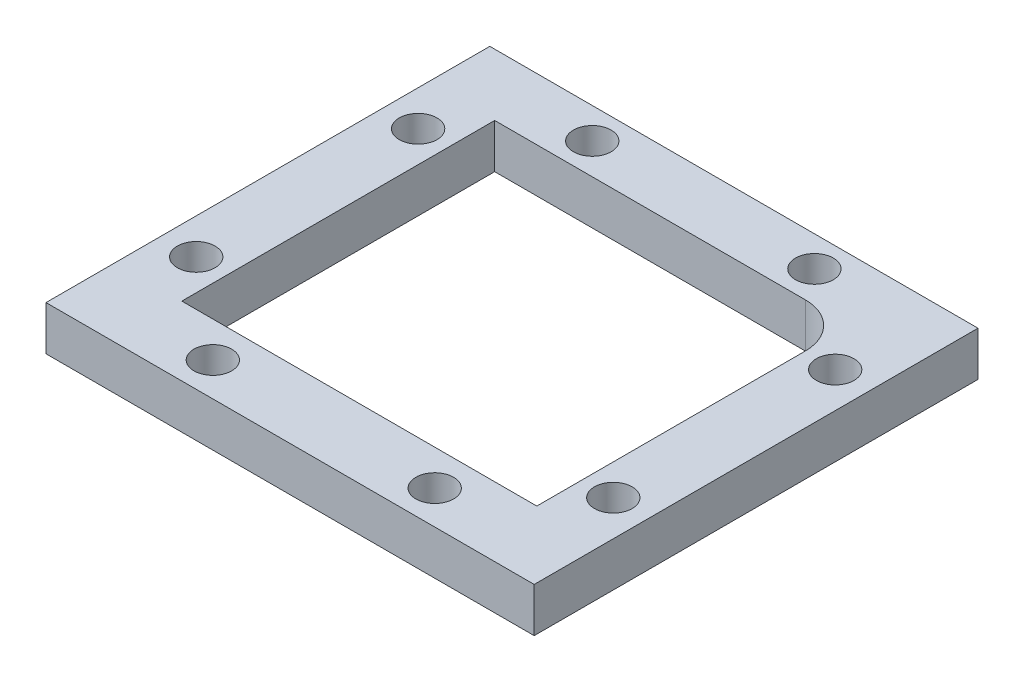
SolidWorks part; units mm, degrees
ref_plane "Alzado" through (0, 0, 0) normal (0, 0, 1) x (1, 0, 0)
ref_plane "Planta" through (0, 0, 0) normal (0, 1, 0) x (1, 0, 0)
ref_plane "Vista lateral" through (0, 0, 0) normal (1, 0, 0) x (0, 0, -1)
sketch "Croquis1" plane through (0, 0, 0) normal (0, 1, 0) x (1, 0, 0)
  line L0 (0, 20) -> (0, -20) construction
  line L1 (-20, 20) -> (20, 20)
  line L2 (-20, 20) -> (-20, -20)
  line L3 (-20, -20) -> (20, -20)
  line L4 (20, 20) -> (20, -20)
  line L5 (-20, 20) -> (20, -20) construction
  line L6 (-20, -20) -> (20, 20) construction
  line L7 (-20, -4.25) -> (-30, -7.25)
  line L8 (-30, -7.25) -> (-30, -15.25)
  line L9 (-30, -15.25) -> (30, -15.25)
  line L10 (20, -4.25) -> (30, -7.25)
  line L11 (30, -7.25) -> (30, -15.25)
  circle A0 centre (-15, 15) radius 2.125
  circle A1 centre (15, 15) radius 2.125
  circle A4 centre (0, 0) radius 15.25
  circle A5 centre (-15, -15) radius 2.125 [skipped]
  circle A6 centre (15, -15) radius 2.125 [skipped]
  point P0 (0, 0)
  point P25 (0, -15.25)
  dimension "D3" = 4.25
  dimension "D7" = 30.5
  dimension "D1" = 40
  dimension "D2" = 40
  dimension "D4" = 5
  dimension "D5" = 2
  dimension "D8" = 8
  dimension "D9" = 10
  dimension "D10" = 15.25
  dimension "D12" = 3
  dimension "D6" = 2
extrude "Soporte caja reductora" add sketch "Croquis1" against normal blind 20
sketch "Croquis3" plane through (0, 0, 15.25) normal (0, 0, 1) x (1, 0, 0)
  line L3 (-20, -20) -> (-20, 0) construction
  circle A0 centre (-23.5, -10) radius 2.125
  circle A1 centre (23.5, -10) radius 2.125
  dimension "D1" = 4.25
  dimension "D2" = 3.5
extrude "Cortar-Extruir1" cut sketch "Croquis3" against normal through all
fillet "Redondeo1" radius 5 2 edges at (-20, -10, -20) (20, -10, -20)
sketch "Sketch1" plane through (0, 0, 0) normal (0, 1, 0) x (1, 0, 0)
  line L0 (15, 20) -> (30, 20)
  line L1 (30, 20) -> (30, 8)
  line L2 (30, 8) -> (25.5, 8)
  line L4 (25.5, 8) -> (25.5, 15)
  line L5 (25.5, 15) -> (20, 15)
  circle A0 centre (15, 15) radius 5
  arc M37 (20, 15) -> (15, 20) centre (15, 15) ccw
  dimension "D1" = 12
  dimension "D2" = 5.5
extrude "Boss-Extrude1" add sketch "Sketch1" along direction (0, 1, 0) on the side against the normal up to surface (20 mm away) contours L5 L4 L2 L1 L0 M37
sketch "Sketch2" plane through (0, 0, -20) normal (0, 0, -1) x (-1, 0, 0)
  line L1 (-20, -20) -> (-20, 0) construction
  circle A0 centre (-22.75, -10) radius 1.625
  dimension "D1" = 3.25
  dimension "D2" = 2.75
extrude "Cut-Extrude1" cut sketch "Sketch2" against normal up to next
sketch "Sketch3" plane through (0, 0, -15) normal (0, 0, 1) x (1, 0, 0)
  line L1 (20, -11.5877) -> (22.75, -13.1754)
  line L2 (22.75, -13.1754) -> (25.5, -11.5877)
  line L3 (25.5, -11.5877) -> (25.5, -8.4123)
  line L4 (25.5, -8.4123) -> (22.75, -6.8246)
  line L5 (22.75, -6.8246) -> (20, -8.4123)
  line L6 (20, -8.4123) -> (20, -11.5877)
  circle A0 centre (22.75, -10) radius 2.75 construction
  dimension "D1" = 5.5
extrude "Cut-Extrude2" cut sketch "Sketch3" against normal blind 2
sketch "Sketch4" plane through (25.5, 0, 0) normal (-1, 0, 0) x (0, 0, 1)
  line L5 (-15, -8.4123) -> (-15, 0) construction
  line L6 (-20, 0) -> (-8, 0) construction
  circle A0 centre (-12.25, -10) radius 1.625
  dimension "D1" = 2.75
  dimension "D2" = 3.25
  dimension "D3" = 10
extrude "Cut-Extrude3" cut sketch "Sketch4" against normal through all
sketch "Sketch5" plane through (30, 0, 0) normal (1, 0, 0) x (0, 0, -1)
  line L1 (15, -11.5877) -> (15, -8.4123)
  line L2 (15, -8.4123) -> (12.25, -6.8246)
  line L3 (12.25, -6.8246) -> (9.5, -8.4123)
  line L4 (9.5, -8.4123) -> (9.5, -11.5877)
  line L5 (9.5, -11.5877) -> (12.25, -13.1754)
  line L6 (12.25, -13.1754) -> (15, -11.5877)
  circle A0 centre (12.25, -10) radius 2.75 construction
  dimension "D1" = 5.5
extrude "Cut-Extrude4" cut sketch "Sketch5" along normal blind 2 from surface
sketch "Croquis6" plane through (0, 0, 0) normal (0, 1, 0) x (1, 0, 0)
  line L0 (-20, -20) -> (20, -20) construction
  line L1 (-15.25, 0) -> (15.25, 0)
  line L2 (-15.25, 0) -> (-15.25, -20)
  line L3 (-15.25, -20) -> (15.25, -20)
  line L4 (15.25, 0) -> (15.25, -20)
  line L6 (-20, -20) -> (20, -20)
  line L7 (-20, -20) -> (-20, -15.25)
  line L8 (-20, -15.25) -> (20, -15.25)
  line L9 (20, -20) -> (20, -15.25)
  circle A0 centre (0, 0) radius 15.25 construction
  circle M5 centre (0, 0) radius 15.25
  line M14 (-20, -15.25) -> (-20, -20)
  line M15 (-20, -20) -> (20, -20)
  line M16 (20, -20) -> (20, -15.25)
extrude "Cortar-Extruir17" cut sketch "Croquis6" against normal through all contours L8 L2 L4 M15 | L8 L2 M14 M15 | L2 L8 M5 | L8 L4 M5 | L8 L4 M15 M16
mirror "Simetría1" about plane through (0, 0, 0) normal (0, 1, 0) of bodies 111
sketch "Croquis7" plane through (0, 0, -20) normal (0, 0, -1) x (-1, 0, 0)
  line L1 (-30, 0) -> (30, 0)
  line L2 (-30, 0) -> (-30, -20)
  line L3 (-30, -20) -> (30, -20)
  line L4 (30, 0) -> (30, -20)
extrude "Cortar-Extruir18" cut sketch "Croquis7" against normal through all
sketch "Croquis8" plane through (0, 20, 0) normal (0, 1, 0) x (1, 0, 0)
  line L3 (-15, 20) -> (30, 20) construction
  line L4 (-11.0405, 13.9391) -> (-10.3152, 11.2321)
  line L5 (10.8174, 13.8793) -> (10.3152, 11.2321)
  line L59 (10.8174, 13.8793) -> (11.9787, 20)
  line L60 (-11.0405, 13.9391) -> (-12.6645, 20)
  line L61 (11.9787, 20) -> (-12.6645, 20)
  circle A0 centre (0, 0) radius 15.25
extrude "Saliente-Extruir2" add sketch "Croquis8" along normal blind 49
sketch "Croquis9" plane through (0, 69, 0) normal (0, 1, 0) x (1, 0, 0)
  line L0 (-20, 0) -> (20, 0)
  line L1 (-20, 15) -> (-20, -4.25) construction
  line L2 (20, 15) -> (20, -4.25) construction
  line L3 (-20, 0) -> (-20, 15)
  line L4 (-15, 20) -> (12.6645, 20)
  line L5 (12.6645, 20) -> (20, 13.9368)
  line L6 (20, 13.9368) -> (20, 0)
  line L7 (20, 0) -> (20.1759, -0.147)
  line L8 (-14.75, 0) -> (-14.75, -15.25)
  line L9 (-15.25, -15.25) -> (-30, -15.25)
  line L10 (-30, -15.25) -> (-30, -7.25)
  line L11 (-30, -7.25) -> (-20, -4.25)
  line L12 (-20, -4.25) -> (-20, 0)
  line L13 (-14.75, -15.25) -> (-15.25, -15.25)
  line L14 (-14.75, -15.25) -> (0, -15.25)
  line L15 (0, -15.25) -> (0, -14.75)
  circle A0 centre (0, 0) radius 14.75
  circle A1 centre (-15, 15) radius 5
  dimension "D1" = 29.5
extrude "Soporte motor" add sketch "Croquis9" against normal blind 15 from offset 15 offset against normal yes
sketch "Croquis12" plane through (0, 0, 15.25) normal (0, 0, 1) x (1, 0, 0)
  line L1 (0, 54) -> (-30, 54) construction
  line L2 (-20, 39) -> (-20, 54) construction
  circle A0 centre (-23.5, 46.5) radius 2.125
  dimension "D3" = 4.25
  dimension "D1" = 7.5
  dimension "D2" = 3.5
extrude "Agujeros de sujecion a base" cut sketch "Croquis12" against normal through all
sketch "Croquis13" plane through (0, 0, 15.25) normal (0, 0, 1) x (1, 0, 0)
  line L1 (-20, 44.4793) -> (-20, 48.5207)
  line L2 (-20, 48.5207) -> (-23.5, 50.5415)
  line L3 (-23.5, 50.5415) -> (-27, 48.5207)
  line L4 (-27, 48.5207) -> (-27, 44.4793)
  line L5 (-27, 44.4793) -> (-23.5, 42.4585)
  line L6 (-23.5, 42.4585) -> (-20, 44.4793)
  circle A0 centre (-23.5, 46.5) radius 3.5 construction
  dimension "D1" = 7
extrude "Tuerca Agujero de sujecion a base" cut sketch "Croquis13" against normal blind 10 from offset 4 offset against normal yes
sketch "Croquis10" plane through (0, 69, 0) normal (0, 1, 0) x (1, 0, 0)
  line L0 (-10.3152, 11.2321) -> (-9.8079, 9.3388)
  line L1 (10.3152, 11.2321) -> (9.4813, 8.1201)
  circle A0 centre (0, 0) radius 14.75
  circle A1 centre (0, 0) radius 15.25
  arc M2 (-10.3152, 11.2321) -> (10.3152, 11.2321) centre (0, 0) cw
extrude "Saliente-Extruir4" add sketch "Croquis10" against normal up to surface (15 mm away) contours A0 L1 L0 M2
sketch "Croquis11" plane through (0, 0, 0) normal (0, -1, 0) x (1, 0, 0)
  line L0 (0, 0) -> (0, -12.6937) construction
  line L1 (15, -20) -> (30, -20)
  line L2 (30, -20) -> (30, 15.25)
  line L3 (30, 15.25) -> (15.25, 15.25)
  line L4 (15.25, 0) -> (15.25, 15.25) construction
  line L5 (15.25, 15.25) -> (30, 15.25) construction
  line L6 (15.25, 15.25) -> (15.25, 4.25)
  line L7 (15.25, 4.25) -> (20, 4.25)
  line L8 (20, 4.25) -> (20, -15)
  circle A0 centre (0, 0) radius 22.5
  circle A1 centre (-15, -15) radius 5
  circle A2 centre (15, -15) radius 5
  line M8 (-15, -20) -> (30, -20)
  line M9 (30, -20) -> (30, -8)
  line M10 (30, -8) -> (25.5, -8)
  line M11 (25.5, -8) -> (25.5, -15)
  line M12 (25.5, -15) -> (20, -15)
  line M14 (20, 4.25) -> (30, 7.25)
  line M15 (30, 7.25) -> (30, 15.25)
  line M16 (30, 15.25) -> (15.25, 15.25)
  line M17 (15.25, 15.25) -> (15.25, 0)
  dimension "D1" = 45
extrude "Cortar-Extruir19" cut sketch "Croquis11" against normal blind 25 contours A0 L3 L7 M14 M17 | A0 M14 M15 M16 | A2 M12 M8 M9 M10 M11
mirror "Simetría2"
sketch "Croquis14" plane through (0, 0, 15.25) normal (0, 0, 1) x (1, 0, 0)
  line L1 (-30, 20) -> (20, 20)
  line L2 (-30, 20) -> (-30, 138)
  line L3 (-30, 138) -> (20, 138)
  line L4 (20, 20) -> (20, 138)
extrude "Cortar-Extruir22" cut sketch "Croquis14" against normal through all
sketch "Croquis15" plane through (0, 0, 0) normal (0, -1, 0) x (1, 0, 0)
  line L0 (-30, 7.25) -> (-30, 15.25) construction
  line L1 (-20, 4.25) -> (-30, 4.25)
  line L2 (-20, 4.25) -> (-20, 11.25)
  line L3 (-20, 11.25) -> (-30, 11.25)
  line L4 (-30, 4.25) -> (-30, 11.25)
  line L5 (-30, 15.25) -> (-15.25, 15.25) construction
  dimension "D1" = 4
extrude "Cortar-Extruir23" cut sketch "Croquis15" against normal through all
sketch "Croquis16" plane through (0, 0, 0) normal (0, -1, 0) x (1, 0, 0)
  line L0 (-15.25, 0) -> (-15.25, 15.25) construction
  line L1 (-30, 15.25) -> (-15.25, 15.25)
  line L2 (-30, 15.25) -> (-30, 12.75)
  line L3 (-20, 12.75) -> (-15.25, 12.75)
  line L4 (-15.25, 15.25) -> (-15.25, 12.75)
  line L5 (-30, 12.75) -> (-30, 11.25)
  line L6 (-30, 11.25) -> (-20, 11.25)
  line L7 (-20, 11.25) -> (-30, 11.25) construction
  line L8 (-20, -15) -> (-20, 11.25) construction
  line L9 (-20, 11.25) -> (-20, 12.75)
  dimension "D1" = 2.5
extrude "Cortar-Extruir24" cut sketch "Croquis16" against normal through all
sketch "Croquis18" plane through (0, 0, -20) normal (0, 0, -1) x (-1, 0, 0)
  line L0 (20, 0) -> (20, 20) construction
  line L1 (-20, 0) -> (20, 0)
  line L2 (-20, 0) -> (-20, 10)
  line L3 (-20, 10) -> (20, 10)
  line L4 (20, 0) -> (20, 10)
  line L5 (15, 20) -> (-15, 20) construction
  dimension "D1" = 10
extrude "Cortar-Extruir25" cut sketch "Croquis18" against normal through all
sketch "Croquis19" plane through (0, 20, 0) normal (0, 1, 0) x (1, 0, 0)
  line L0 (-20, -12.75) -> (-34, -12.75)
  line L1 (-34, -12.75) -> (-34, -7.75)
  line L2 (-34, -7.75) -> (-24, -7.75)
  line L3 (-24, -7.75) -> (-20, -3.75)
  line L4 (-20, 15) -> (-20, -12.75) construction
  line L5 (-20, -3.75) -> (-20, -12.75)
  dimension "D1" = 5
  dimension "D2" = 4
  dimension "D3" = 4
  dimension "D4" = 10
extrude "Saliente-Extruir5" add sketch "Croquis19" against normal up to surface (10 mm away) up to face at (15, 10, -12.875)
sketch "Croquis20" plane through (0, 0, 7.75) normal (0, 0, -1) x (-1, 0, 0)
  circle A0 centre (29, 15) radius 1
  dimension "D1" = 2
extrude "Cortar-Extruir26" cut sketch "Croquis20" against normal through all
sketch "Croquis21" plane through (20, 0, 0) normal (1, 0, 0) x (0, 0, -1)
  line L1 (20, 20) -> (20, 10) construction
  circle A0 centre (4.75, 15) radius 1.625
  dimension "D1" = 3.25
  dimension "D2" = 15.25
extrude "Cortar-Extruir27" cut sketch "Croquis21" against normal up to next
sketch "Croquis22" plane through (0, 10, 0) normal (0, -1, 0) x (1, 0, 0)
  circle A0 centre (-15, -15) radius 2.125
  circle A1 centre (15, -15) radius 2.125
  circle A2 centre (15, -15) radius 1
  circle A3 centre (-15, -15) radius 1
  dimension "D1" = 2
extrude "Saliente-Extruir6" add sketch "Croquis22" against normal blind 10
sketch "Croquis23" plane through (0, 0, -20) normal (0, 0, -1) x (-1, 0, 0)
  circle A0 centre (0, 15) radius 1.625
  dimension "D1" = 3.25
extrude "Cortar-Extruir28" cut sketch "Croquis23" against normal through all
sketch "Croquis24" plane through (0, 0, -20) normal (0, 0, -1) x (-1, 0, 0)
  line L1 (1.5877, 12.25) -> (3.1754, 15)
  line L2 (3.1754, 15) -> (1.5877, 17.75)
  line L3 (1.5877, 17.75) -> (-1.5877, 17.75)
  line L4 (-1.5877, 17.75) -> (-3.1754, 15)
  line L5 (-3.1754, 15) -> (-1.5877, 12.25)
  line L6 (-1.5877, 12.25) -> (1.5877, 12.25)
  circle A0 centre (0, 15) radius 2.75 construction
  dimension "D1" = 5.5
extrude "Cortar-Extruir29" cut sketch "Croquis24" against normal blind 10 from offset 3 offset against normal yes
sketch "Croquis26" plane through (0, 10, 0) normal (0, -1, 0) x (1, 0, 0)
  line L0 (-29, 12.75) -> (-58.825, 12.75)
  line L1 (-58.825, 12.75) -> (-39.1605, -4.1045)
  line L3 (-39.5945, 1.5357) -> (-46.8449, 7.75)
  line L4 (-46.8449, 7.75) -> (-34.2682, 7.75)
  line L5 (-34.2682, 7.75) -> (-39.5945, 1.5357)
  line L7 (-29, 7.75) -> (-35.7321, -0.1045)
  line L8 (-29, 7.75) -> (-29, 12.75)
  line L9 (-34, 7.75) -> (-24, 7.75) construction
  line L10 (-34, 12.75) -> (-15.25, 12.75) construction
  line L11 (-39.1605, -4.1045) -> (-20, -4.1045)
  line L12 (-20, 3.75) -> (-20, -15) construction
  line L13 (-20, -4.1045) -> (-20, -0.1045)
  line L14 (-20, -0.1045) -> (-35.7321, -0.1045)
  dimension "D1" = 4
  dimension "D2" = 4
  dimension "D3" = 4
  dimension "D4" = 29.825
  dimension "D5" = 40.6
extrude "Saliente-Extruir7" add sketch "Croquis26" against normal blind 10
sketch "Croquis27" plane through (0, 0, 12.75) normal (0, 0, 1) x (1, 0, 0)
  line L0 (-29, 16) -> (-29, 14) construction
  line L1 (-46.8449, 20) -> (-46.8449, 10) construction
  circle A0 centre (-40.5449, 15) radius 1.625
  circle A2 centre (-29, 15) radius 1.625
  dimension "D1" = 3.25
  dimension "D2" = 6.3
extrude "Cortar-Extruir30" cut sketch "Croquis27" against normal up to next
sketch "Croquis28" plane through (0, 0, 12.75) normal (0, 0, 1) x (1, 0, 0)
  line L1 (-38.9572, 12.25) -> (-37.3694, 15)
  line L2 (-37.3694, 15) -> (-38.9572, 17.75)
  line L3 (-38.9572, 17.75) -> (-42.1326, 17.75)
  line L4 (-42.1326, 17.75) -> (-43.7203, 15)
  line L5 (-43.7203, 15) -> (-42.1326, 12.25)
  line L6 (-42.1326, 12.25) -> (-38.9572, 12.25)
  line L7 (-27.4123, 12.25) -> (-25.8246, 15)
  line L8 (-25.8246, 15) -> (-27.4123, 17.75)
  line L9 (-27.4123, 17.75) -> (-30.5877, 17.75)
  line L10 (-30.5877, 17.75) -> (-32.1754, 15)
  line L11 (-32.1754, 15) -> (-30.5877, 12.25)
  line L12 (-30.5877, 12.25) -> (-27.4123, 12.25)
  circle A0 centre (-40.5449, 15) radius 2.75 construction
  circle A1 centre (-29, 15) radius 2.75 construction
  dimension "D1" = 5.5
extrude "Cortar-Extruir31" cut sketch "Croquis28" against normal up to next from offset 3 offset against normal yes
sketch "Croquis29" plane through (-18.6128, 0, -21.716) normal (-0.6508, 0, -0.7593) x (-0.7593, 0, 0.6508)
  line L2 (31.0624, 20) -> (31.0624, 10) construction
  circle A0 centre (33.8124, 15) radius 1.625
  dimension "D2" = 3.25
  dimension "D1" = 2.75
extrude "Cortar-Extruir32" cut sketch "Croquis29" against normal up to next
sketch "Croquis31" plane through (-18.6128, 0, -21.716) normal (-0.6508, 0, -0.7593) x (-0.7593, 0, 0.6508)
  line L1 (36.5624, 16.5877) -> (33.8124, 18.1754)
  line L2 (33.8124, 18.1754) -> (31.0624, 16.5877)
  line L3 (31.0624, 16.5877) -> (31.0624, 13.4123)
  line L4 (31.0624, 13.4123) -> (33.8124, 11.8246)
  line L5 (33.8124, 11.8246) -> (36.5624, 13.4123)
  line L6 (36.5624, 13.4123) -> (36.5624, 16.5877)
  circle A0 centre (33.8124, 15) radius 2.75 construction
  dimension "D1" = 5.5
extrude "Cortar-Extruir33" cut sketch "Croquis31" against normal up to next from offset 2.5 offset against normal yes
sketch "Croquis35" plane through (0, 20, 0) normal (0, 1, 0) x (1, 0, 0)
  line L0 (-15, 20) -> (15, 20) construction
  line L1 (10.3896, 0) -> (23.695, 0)
  line L2 (10.3896, 0) -> (10.3896, -6.8269)
  line L3 (10.3896, -6.8269) -> (23.695, -6.8269)
  line L4 (23.695, 0) -> (23.695, -6.8269)
  dimension "D1" = 20
extrude "Cortar-Extruir34" cut sketch "Croquis35" against normal through all both and the other way through all
sketch "Croquis36" plane through (20, 0, 0) normal (1, 0, 0) x (0, 0, -1)
  line L1 (7.5, 16.5877) -> (4.75, 18.1754)
  line L2 (4.75, 18.1754) -> (2, 16.5877)
  line L3 (2, 16.5877) -> (2, 13.4123)
  line L4 (2, 13.4123) -> (4.75, 11.8246)
  line L5 (4.75, 11.8246) -> (7.5, 13.4123)
  line L6 (7.5, 13.4123) -> (7.5, 16.5877)
  circle A0 centre (4.75, 15) radius 2.75 construction
  dimension "D1" = 5.5
extrude "Cortar-Extruir35" cut sketch "Croquis36" against normal blind 10 from offset 3 offset against normal yes
sketch "Croquis37" plane through (0, 10, 0) normal (0, -1, 0) x (1, 0, 0)
  line L0 (-39.1605, -4.1045) -> (-20.6149, -20)
  line L1 (-20.6149, -20) -> (-15, -20)
  line L2 (-33.014, -4.1045) -> (-19.5581, -15.6376)
  line L3 (-39.1605, -4.1045) -> (-20, -4.1045) construction
  line L4 (-19.5581, -15.6376) -> (-15, -20)
  line L5 (-58.825, 12.75) -> (-39.1605, -4.1045) construction
  line L6 (-39.5945, 1.5357) -> (-46.8449, 7.75) construction
  line L7 (-39.1605, -4.1045) -> (-33.014, -4.1045)
extrude "Saliente-Extruir8" add sketch "Croquis37" against normal blind 10
sketch "Croquis38" plane through (0, 10, 0) normal (0, -1, 0) x (1, 0, 0)
  line L0 (-58.825, 12.75) -> (-38.825, 12.75)
  line L1 (-58.825, 12.75) -> (-15.25, 12.75) construction
  line L2 (-38.825, 12.75) -> (-38.825, 9.75)
  line L3 (-38.825, 9.75) -> (-55.3248, 9.75)
  line L4 (-58.825, 12.75) -> (-20.6149, -20) construction
  line L5 (-55.3248, 9.75) -> (-58.825, 12.75)
  dimension "D1" = 3
  dimension "D2" = 20
extrude "Saliente-Extruir9" add sketch "Croquis38" along normal blind 13
sketch "Croquis39" plane through (0, 10, 0) normal (0, -1, 0) x (1, 0, 0)
  line L0 (-38.825, 9.75) -> (-38.825, 7.75)
  line L1 (-46.8449, 7.75) -> (-34.2682, 7.75) construction
  line L3 (-55.3248, 9.75) -> (-20.6149, -20) construction
  line L4 (-52.9914, 7.75) -> (-55.3248, 9.75)
  line L5 (-55.3248, 9.75) -> (-38.825, 9.75)
  line L6 (-52.9914, 7.75) -> (-50.658, 5.75)
  line L7 (-50.658, 5.75) -> (-38.825, 5.75)
  line L8 (-38.825, 5.75) -> (-38.825, 7.75)
  dimension "D1" = 2
extrude "Saliente-Extruir10" add sketch "Croquis39" along normal blind 3
mirror "Simetría3" of bodies 142
sketch "Croquis40" plane through (0, 0, -20) normal (0, 0, -1) x (-1, 0, 0)
  line L1 (-30.8963, 20) -> (75.6873, 20)
  line L2 (-30.8963, 20) -> (-30.8963, -27.3915)
  line L3 (-30.8963, -27.3915) -> (75.6873, -27.3915)
  line L4 (75.6873, 20) -> (75.6873, -27.3915)
extrude "Cortar-Extruir36" cut sketch "Croquis40" against normal through all both and the other way through all
sketch "Croquis41" plane through (0, 20, 0) normal (0, -1, 0) x (1, 0, 0)
  line L0 (-19.993, -22.3025) -> (-20, 3.75)
  line L1 (-20, 3.75) -> (-24, 7.75)
  line L2 (-24, 7.75) -> (-56.0351, 7.75)
  line L3 (-56.0351, 7.75) -> (-19.993, -22.3025)
extrude "Cortar-Extruir37" cut sketch "Croquis41" against normal through all both and the other way through all
sketch "Croquis42" plane through (0, 0, 9.75) normal (0, 0, -1) x (-1, 0, 0)
  line L0 (46.7203, 20) -> (46.7203, 30)
  line L1 (52.9914, 20) -> (24, 20) construction
  line L2 (46.7203, 30) -> (38.825, 30)
  line L3 (38.825, 30) -> (33.493, 43.7606)
  line L4 (33.493, 43.7606) -> (49.5253, 48.9514)
  line L5 (49.5253, 48.9514) -> (67.2004, 42.5122)
  line L6 (67.2004, 42.5122) -> (65.9066, 20)
  line L7 (65.9066, 20) -> (51.714, 13.8642)
  line L8 (51.714, 13.8642) -> (46.7203, 20)
  dimension "D1" = 3
extrude "Cortar-Extruir38" cut sketch "Croquis42" against normal through all both and the other way through all
sketch "Croquis43" plane through (0, 20, 0) normal (0, -1, 0) x (1, 0, 0)
  line L0 (-19.9936, -20) -> (-46.7203, 7.75)
  line L1 (-19.9936, -20) -> (-17.1126, -17.2252)
  line L2 (-46.7203, 7.75) -> (-43.8393, 10.5248)
  line L3 (-17.1126, -17.2252) -> (-43.8393, 10.5248)
  dimension "D1" = 4
extrude "Saliente-Extruir11" add sketch "Croquis43" against normal up to vertex (10 mm away)
sketch "Croquis44" plane through (0, 0, 9.75) normal (0, 0, -1) x (-1, 0, 0)
  line L7 (38.9572, 27.75) -> (37.3694, 25)
  line L8 (37.3694, 25) -> (38.9572, 22.25)
  line L9 (38.9572, 22.25) -> (42.1326, 22.25)
  line L10 (42.1326, 22.25) -> (43.7203, 25)
  line L11 (43.7203, 25) -> (42.1326, 27.75)
  line L12 (42.1326, 27.75) -> (38.9572, 27.75)
  circle A1 centre (40.5449, 25) radius 2.75 construction
extrude "Cortar-Extruir39" cut sketch "Croquis44" along normal through all
sketch "Croquis45" plane through (0, 0, 12.75) normal (0, 0, 1) x (1, 0, 0)
  line L1 (-46.7203, 30) -> (-15.25, 30)
  line L2 (-46.7203, 30) -> (-46.7203, 20)
  line L3 (-46.7203, 20) -> (-15.25, 20)
  line L4 (-15.25, 30) -> (-15.25, 20)
  circle A0 centre (-40.5449, 25) radius 1.625
  circle A1 centre (-29, 25) radius 1.625
extrude "Saliente-Extruir12" add sketch "Croquis45" along normal blind 2.5
sketch "Croquis46" plane through (0, 20, 0) normal (0, -1, 0) x (1, 0, 0)
  line L0 (15.25, 0) -> (20, 0)
  line L1 (20, 0) -> (20, 15.25)
  line L2 (-46.7203, 15.25) -> (-15.25, 15.25) construction
  line L3 (20, 15.25) -> (7.5498, 15.25)
  line L4 (7.5498, 15.25) -> (7.5498, 13.25)
  line L5 (-15.25, 0) -> (-15.25, 15.25)
  line L6 (-15.25, 15.25) -> (-7.5498, 15.25)
  line L7 (-7.5498, 15.25) -> (-7.5498, 13.25)
  arc A0 (-7.5498, 13.25) -> (-15.25, 0) centre (0, 0) ccw
  arc A1 (15.25, 0) -> (7.5498, 13.25) centre (0, 0) ccw
  dimension "D1" = 2
extrude "Saliente-Extruir13" add sketch "Croquis46" against normal up to vertex (10 mm away)
sketch "Croquis47" plane through (0, 0, 15.25) normal (0, 0, 1) x (1, 0, 0)
  line L1 (15.4123, 22.3525) -> (17, 25.1025)
  line L2 (17, 25.1025) -> (15.4123, 27.8525)
  line L3 (15.4123, 27.8525) -> (12.2369, 27.8525)
  line L4 (12.2369, 27.8525) -> (10.6491, 25.1025)
  line L5 (10.6491, 25.1025) -> (12.2369, 22.3525)
  line L6 (12.2369, 22.3525) -> (15.4123, 22.3525)
  line L10 (20, 30) -> (20, 20) construction
  line L11 (0, 20) -> (0, 0) construction
  line L12 (-15.25, 20) -> (15.25, 20) construction
  line L13 (-12.2369, 22.3525) -> (-15.4123, 22.3525)
  line L14 (-10.6491, 25.1025) -> (-12.2369, 22.3525)
  line L15 (-12.2369, 27.8525) -> (-10.6491, 25.1025)
  line L16 (-15.4123, 27.8525) -> (-12.2369, 27.8525)
  line L17 (-17, 25.1025) -> (-15.4123, 27.8525)
  line L18 (-15.4123, 22.3525) -> (-17, 25.1025)
  circle A0 centre (13.8246, 25.1025) radius 2.75 construction
  circle A1 centre (13.8246, 25.1025) radius 1.625
  circle A2 centre (-13.8246, 25.1025) radius 2.75 construction
  circle A3 centre (-13.8246, 25.1025) radius 1.625
  dimension "D1" = 3.25
  dimension "D2" = 5.5
  dimension "D3" = 3
extrude "Cortar-Extruir40" cut sketch "Croquis47" against normal blind 10 from offset 2 offset against normal yes
sketch "Croquis48" plane through (0, 0, 15.25) normal (0, 0, 1) x (1, 0, 0)
  circle A0 centre (13.8246, 25.1025) radius 1.625
  circle A1 centre (-13.8246, 25.1025) radius 1.625
extrude "Cortar-Extruir41" cut sketch "Croquis48" against normal up to vertex
sketch "Croquis49" plane through (0, 20, 0) normal (0, -1, 0) x (1, 0, 0)
  line L1 (-19.9936, -20) -> (-54.7897, -20)
  line L2 (-19.9936, -20) -> (-19.9936, 22.211)
  line L3 (-19.9936, 22.211) -> (-54.7897, 22.211)
  line L4 (-54.7897, -20) -> (-54.7897, 22.211)
extrude "Cortar-Extruir42" cut sketch "Croquis49" against normal through all both and the other way through all
sketch "Croquis51" plane through (0, 30, 0) normal (0, 1, 0) x (1, 0, 0)
  circle A0 centre (0, 0) radius 15.25
  circle A1 centre (0, 0) radius 14.25
  dimension "D1" = 28.5
extrude "Saliente-Extruir14" add sketch "Croquis51" against normal blind 10
sketch "Croquis52" plane through (0, 0, 13.25) normal (0, 0, -1) x (-1, 0, 0)
  line L1 (-10.6491, 25.1025) -> (-12.2369, 27.8525)
  line L2 (-12.2369, 27.8525) -> (-15.4123, 27.8525)
  line L3 (-15.4123, 27.8525) -> (-17, 25.1025)
  line L4 (-17, 25.1025) -> (-15.4123, 22.3525)
  line L5 (-15.4123, 22.3525) -> (-12.2369, 22.3525)
  line L6 (-12.2369, 22.3525) -> (-10.6491, 25.1025)
  line L7 (17, 25.1025) -> (15.4123, 27.8525)
  line L8 (15.4123, 27.8525) -> (12.2369, 27.8525)
  line L9 (12.2369, 27.8525) -> (10.6491, 25.1025)
  line L10 (10.6491, 25.1025) -> (12.2369, 22.3525)
  line L11 (12.2369, 22.3525) -> (15.4123, 22.3525)
  line L12 (15.4123, 22.3525) -> (17, 25.1025)
  circle A0 centre (-13.8246, 25.1025) radius 2.75 construction
  circle A1 centre (13.8246, 25.1025) radius 2.75 construction
extrude "Cortar-Extruir43" cut sketch "Croquis52" along normal blind 10
sketch "Croquis53" plane through (0, 0, -17) normal (0, 0, 1) x (1, 0, 0)
  line L1 (3.1754, 25) -> (1.5877, 27.75)
  line L2 (1.5877, 27.75) -> (-1.5877, 27.75)
  line L3 (-1.5877, 27.75) -> (-3.1754, 25)
  line L4 (-3.1754, 25) -> (-1.5877, 22.25)
  line L5 (-1.5877, 22.25) -> (1.5877, 22.25)
  line L6 (1.5877, 22.25) -> (3.1754, 25)
  circle A0 centre (0, 25) radius 2.75 construction
extrude "Cortar-Extruir44" cut sketch "Croquis53" along normal blind 10
sketch "Croquis54" plane through (17, 0, 0) normal (-1, 0, 0) x (0, 0, 1)
  line L1 (-4.75, 28.1754) -> (-7.5, 26.5877)
  line L2 (-7.5, 26.5877) -> (-7.5, 23.4123)
  line L3 (-7.5, 23.4123) -> (-4.75, 21.8246)
  line L4 (-4.75, 21.8246) -> (-2, 23.4123)
  line L5 (-2, 23.4123) -> (-2, 26.5877)
  line L6 (-2, 26.5877) -> (-4.75, 28.1754)
  circle A0 centre (-4.75, 25) radius 2.75 construction
extrude "Cortar-Extruir45" cut sketch "Croquis54" along normal blind 10
sketch "Croquis55" plane through (0, 30, 0) normal (0, 1, 0) x (1, 0, 0)
  line L0 (-7.5498, -15.25) -> (7.5498, -15.25)
  line L1 (7.5498, -15.25) -> (7.5498, -13.25)
  line L2 (-7.5498, -15.25) -> (-7.5498, -13.25)
  arc A0 (-7.5498, -13.25) -> (7.5498, -13.25) centre (0, 0) ccw
  line M5 (-7.5498, -15.25) -> (-7.5498, -13.25)
  arc M6 (-7.5498, -13.25) -> (7.5498, -13.25) centre (0, 0) ccw
  line M7 (7.5498, -13.25) -> (7.5498, -15.25)
extrude "Saliente-Extruir15" add sketch "Croquis55" against normal blind 10 contours L0 M5 M6 | L0 M6 M7
sketch "Croquis56" plane through (0, 30, 0) normal (0, 1, 0) x (1, 0, 0)
  line L5 (-27.5, -23.0435) -> (27.5, -23.0435)
  line L6 (-27.5, -23.0435) -> (-27.5, 26.9565)
  line L7 (-27.5, 26.9565) -> (27.5, 26.9565)
  line L8 (20, -15.25) -> (20, 15)
  line L9 (15, 20) -> (-19.9936, 20)
  line L10 (-19.9936, 20) -> (-19.9936, -15.25)
  line L11 (-19.9936, -15.25) -> (20, -15.25)
  line L12 (20, -15.25) -> (20, 15)
  line L13 (15, 20) -> (-19.9936, 20)
  line L14 (-19.9936, 20) -> (-19.9936, -15.25)
  line L15 (-19.9936, -15.25) -> (20, -15.25)
  line L16 (27.5, -23.0435) -> (27.5, 26.9565)
  line L17 (-27.5, -23.0435) -> (27.5, 26.9565) construction
  line L18 (-27.5, 26.9565) -> (27.5, -23.0435) construction
  arc A2 (20, 15) -> (15, 20) centre (15, 15) ccw
  arc A3 (20, 15) -> (15, 20) centre (15, 15) ccw
  point P0 (0, 1.9565)
  dimension "D2" = 50
  dimension "D3" = 55
  dimension "D1" = 0
extrude "Saliente-Extruir16" add sketch "Croquis56" along normal blind 5 separate body
sketch "Croquis57" plane through (-27.5, 0, 0) normal (-1, 0, 0) x (0, 0, 1)
  line L1 (-20, 30) -> (22.652, 30)
  line L2 (-20, 30) -> (-20, 17.1978)
  line L3 (-20, 17.1978) -> (22.652, 17.1978)
  line L4 (22.652, 30) -> (22.652, 17.1978)
extrude "Cortar-Extruir46" cut sketch "Croquis57" against normal through all both and the other way through all
sketch "Croquis58" plane through (0, 30, 0) normal (0, -1, 0) x (1, 0, 0)
  line L0 (-19.9936, 15.25) -> (20, 15.25) construction
  line L1 (-19.9936, -2.375) -> (35.5888, -2.375) construction
  line L2 (-19.9936, -20) -> (-19.9936, 15.25) construction
  line L3 (15, -20) -> (-19.9936, -20) construction
  line L4 (0, 0) -> (0, -15.5362) construction
  circle A0 centre (-12.5, 19.25) radius 2.125
  circle A1 centre (12.5, 19.25) radius 2.125
  circle A2 centre (-12.5, -23.5) radius 2.125
  circle A3 centre (12.5, -23.5265) radius 2.125
  circle A4 centre (-23.4936, 10.125) radius 2.125
  circle A5 centre (-23.4936, -14.875) radius 2.125
  circle A6 centre (23.4936, -14.875) radius 2.125
  circle A7 centre (23.4936, 10.125) radius 2.125
  dimension "D2" = 4.25
  dimension "D4" = 12.5
  dimension "D6" = 3.5
  dimension "D8" = 12.5
  dimension "D1" = 4
  dimension "D3" = 12.5
  dimension "D5" = 3.5
  dimension "D7" = 12.5
extrude "Cortar-Extruir47" cut sketch "Croquis58" against normal blind 5
